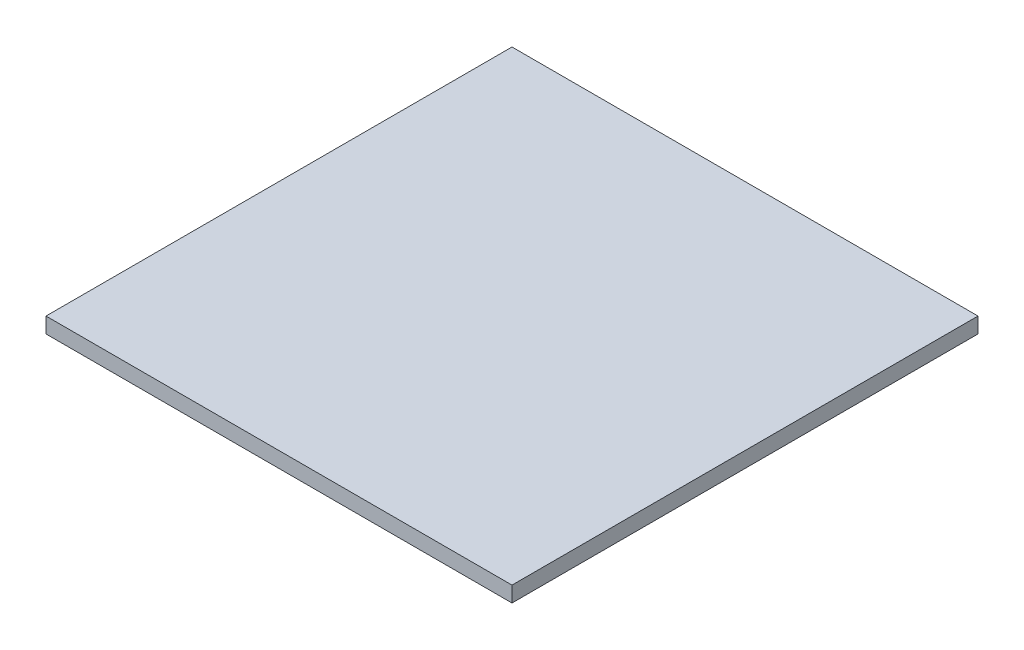
SolidWorks part; units mm, degrees
ref_plane "Front Plane" through (0, 0, 0) normal (0, 0, 1) x (1, 0, 0)
ref_plane "Top Plane" through (0, 0, 0) normal (0, 1, 0) x (1, 0, 0)
ref_plane "Right Plane" through (0, 0, 0) normal (1, 0, 0) x (0, 0, -1)
sketch "Sketch1" plane through (0, 0, 0) normal (0, 1, 0) x (1, 0, 0)
  line L1 (-300, -300) -> (300, -300)
  line L2 (-300, -300) -> (-300, 300)
  line L3 (-300, 300) -> (300, 300)
  line L4 (300, -300) -> (300, 300)
  line L5 (-300, -300) -> (300, 300) construction
  line L6 (-300, 300) -> (300, -300) construction
  point P0 (0, 0)
  dimension "D1" = 600
  dimension "D2" = 600
extrude "Boss-Extrude1" add sketch "Sketch1" along normal mid plane 20
